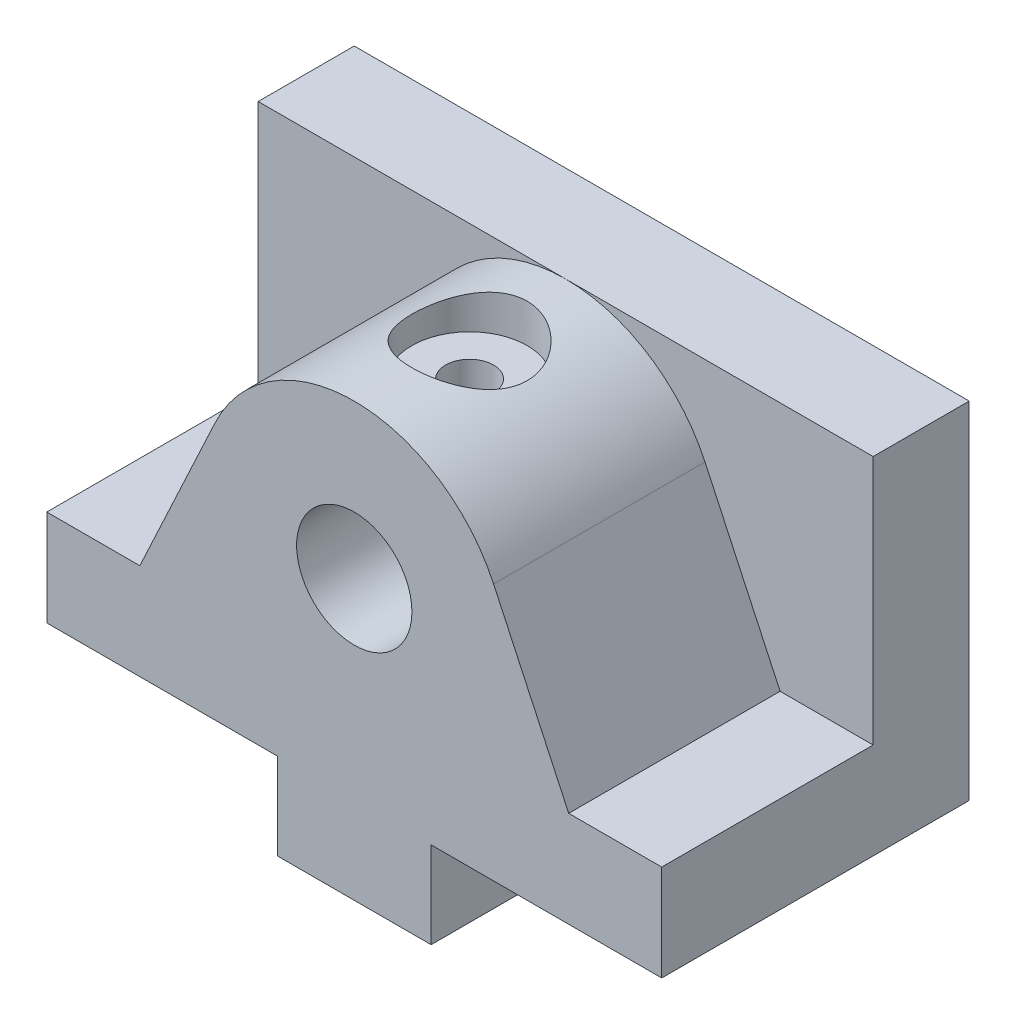
SolidWorks part; units mm, degrees
ref_plane "Front Plane" through (0, 0, 0) normal (0, 0, 1) x (1, 0, 0)
ref_plane "Top Plane" through (0, 0, 0) normal (0, 1, 0) x (1, 0, 0)
ref_plane "Right Plane" through (0, 0, 0) normal (1, 0, 0) x (0, 0, -1)
sketch "Sketch1" plane through (0, 0, 0) normal (0, 0, 1) x (1, 0, 0)
  line L0 (0, -45) -> (0, 45) construction
  line L1 (-32, 9) -> (-8, 9)
  line L2 (-32, 9) -> (-32, 45)
  line L3 (-32, 45) -> (32, 45)
  line L4 (32, 9) -> (32, 45)
  line L6 (-8, 9) -> (-8, 0)
  line L7 (-8, 0) -> (8, 0)
  line L8 (8, 9) -> (8, 0)
  line L9 (8, 9) -> (32, 9)
  point P12 (0, 0)
  dimension "D1" = 64
  dimension "D2" = 9
  dimension "D3" = 36
  dimension "D4" = 16
extrude "Boss-Extrude1" add sketch "Sketch1" along normal blind 10
sketch "Sketch3" plane through (0, 0, 10) normal (0, 0, 1) x (1, 0, 0)
  line L0 (-32, 9) -> (-32, 19)
  line L1 (-32, 19) -> (-22.3171, 19)
  line L2 (-22.3171, 19) -> (-14.5009, 35.7619)
  line L3 (14.5009, 35.7619) -> (22.3171, 19)
  line L4 (22.3171, 19) -> (32, 19)
  line L5 (32, 9) -> (32, 45) construction
  line L6 (32, 19) -> (32, 9)
  line L7 (-32, 19) -> (-32, 9)
  line L8 (-32, 45) -> (-32, 9)
  line L9 (-32, 9) -> (-8, 9)
  line L10 (-8, 9) -> (-8, 0)
  line L11 (-8, 0) -> (8, 0)
  line L12 (8, 0) -> (8, 9)
  line L13 (8, 9) -> (32, 9)
  line L14 (32, 9) -> (32, 45)
  line L15 (32, 45) -> (-32, 45)
  line L16 (-32, 19) -> (-32, 9)
  line L17 (-32, 9) -> (-8, 9)
  line L18 (-8, 9) -> (-8, 0)
  line L19 (-8, 0) -> (8, 0)
  line L20 (8, 0) -> (8, 9)
  line L21 (8, 9) -> (32, 9)
  line L24 (32, 45) -> (-32, 45) construction
  arc A0 (-14.5009, 35.7619) -> (14.5009, 35.7619) centre (0, 29) cw
  line M13 (-32, 45) -> (-32, 9)
  line M14 (-32, 9) -> (-8, 9)
  line M15 (-8, 9) -> (-8, 0)
  line M16 (-8, 0) -> (8, 0)
  line M17 (8, 0) -> (8, 9)
  line M18 (8, 9) -> (32, 9)
  line M19 (32, 9) -> (32, 45)
  dimension "D4" = 16
  dimension "D2" = 10
  dimension "D3" = 50
  dimension "D1" = 0
extrude "Boss-Extrude2" add sketch "Sketch3" along normal blind 22 contours A0 L2 L1 L4 L3 M13 M14 M15 M16 M17 M18 M19
hole_wizard "Ø12.0mm Dowel Hole1" positions "Sketch4" profile "Sketch5" hole size "Ø12.0" standard "ANSI Metric"
sketch "Sketch4" plane through (0, 0, 32) normal (0, 0, 1) x (1, 0, 0)
  arc A0 (14.5009, 35.7619) -> (0, 45) centre (0, 29) ccw construction
  point P0 (0, 29)
sketch "Sketch5" plane through (0, 29, 32) normal (1, 0, 0) x (0, -1, 0)
  line L0 (0, 0) -> (0, 24)
  line L1 (0, 24) -> (6, 20.3948)
  line L2 (6, 20.3948) -> (6, 0)
  line L5 (6, 0) -> (0, 0)
  line L10 (0, 24) -> (-6, 20.3948) construction
  line L11 (0, -6.35) -> (0, 107.95) construction
  dimension "Hole Dia." = 12
  dimension "Hole Depth" = 24
  dimension "Drill Angle" = 118
hole_wizard "Tap Drill for M6x1.0 Tap1" positions "Sketch6" profile "Sketch7" hole size "M6x1.0" standard "ANSI Metric"
sketch "Sketch6" plane through (0, 0, 0) normal (0, -1, 0) x (-1, 0, 0)
  line L0 (0, 0) -> (0, -32) construction
  line L1 (8, -32) -> (-8, -32) construction
  point P0 (0, -8)
  point P2 (0, -24)
  dimension "D1" = 16
  dimension "D2" = 8
sketch "Sketch7" plane through (0, 0, 8) normal (1, 0, 0) x (0, 0, -1)
  line L0 (0, 0) -> (0, 17.5022)
  line L1 (0, 17.5022) -> (2.5, 16)
  line L2 (2.5, 16) -> (2.5, 0)
  line L5 (2.5, 0) -> (0, 0)
  line L10 (0, 17.5022) -> (-2.5, 16) construction
  line L11 (0, -6.35) -> (0, 107.95) construction
  dimension "Hole Dia." = 5
  dimension "Hole Depth" = 16
  dimension "Drill Angle" = 118
hole_wizard "Tap Drill for M6x1.0 Tap3" positions "3DSketch3" profile "Sketch10" hole size "M6x1.0" standard "ANSI Metric"
sketch3d "3DSketch3"
  line L0 (32, 45, 0) -> (-32, 45, 0) construction
  point P3 (0, 45, 20)
  dimension "D1" = 20
sketch "Sketch10" plane through (0, 45, 20) normal (1, 0, 0) x (0, 0, 1)
  line L0 (0, 0) -> (0, 17.5022)
  line L1 (0, 17.5022) -> (2.5, 16)
  line L2 (2.5, 16) -> (2.5, 0.021)
  line L3 (2.5, 0.021) -> (2.525, 0)
  line L5 (2.525, 0) -> (0, 0)
  line L6 (-2.5, 0.021) -> (-2.525, 0) construction
  line L10 (0, 17.5022) -> (-2.5, 16) construction
  line L11 (0, -6.35) -> (0, 107.95) construction
  dimension "Hole Dia." = 5
  dimension "Hole Depth" = 16
  dimension "Near C'Sink Dia." = 5.05
  dimension "Near C'Sink Angle" = 100
  dimension "Drill Angle" = 118
sketch "Sketch13" plane through (0, 45, 0) normal (0, 1, 0) x (1, 0, 0)
  circle A0 centre (0, -20) radius 6
  dimension "D1" = 12
extrude "Cut-Extrude1" cut sketch "Sketch13" against normal blind 4
